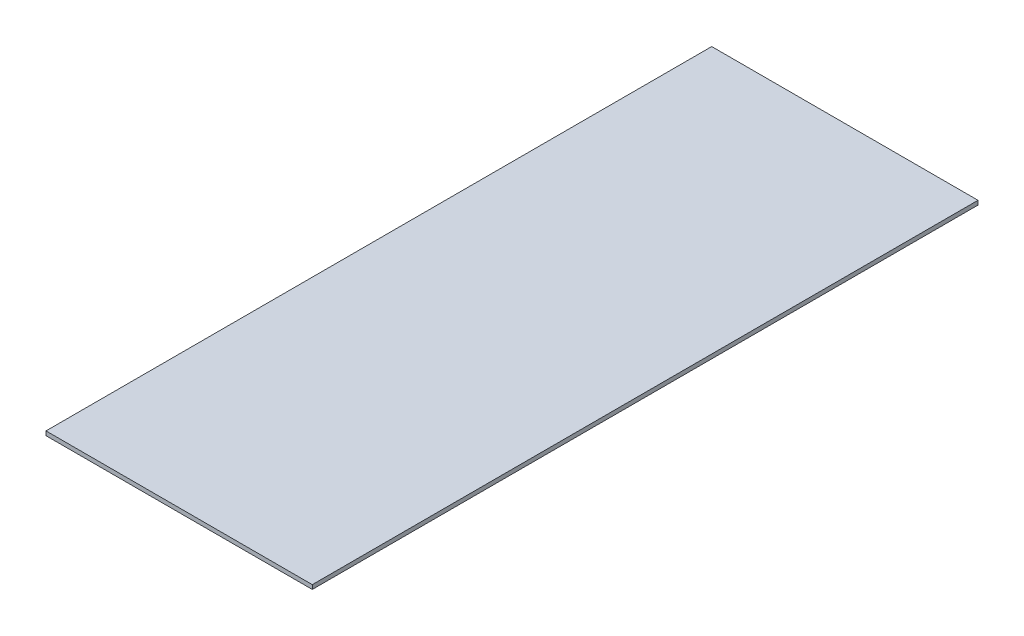
SolidWorks part; units mm, degrees
material "ABS"
ref_plane "Front Plane" through (0, 0, 0) normal (0, 0, 1) x (1, 0, 0)
ref_plane "Top Plane" through (0, 0, 0) normal (0, 1, 0) x (1, 0, 0)
ref_plane "Right Plane" through (0, 0, 0) normal (1, 0, 0) x (0, 0, -1)
sketch "Sketch1" plane through (0, 0, 0) normal (0, 1, 0) x (1, 0, 0)
  line L1 (0, 0) -> (202, 0)
  line L2 (0, 0) -> (0, 505)
  line L3 (0, 505) -> (202, 505)
  line L4 (202, 0) -> (202, 505)
  dimension "D1" = 202
  dimension "D2" = 505
extrude "Boss-Extrude1" add sketch "Sketch1" along normal blind 3.175
equation "\"ABS_thickness\" = 1.59\t"
equation "\"ABS_thickness_1/8\" = 3.175\t"
equation "\"Bus_bar_thickness\" = 3.175"
equation "\"Connector_width\" = 20.2"
equation "\"Number_of_cells_long\" = 25"
equation "\"Number_of_cells_wide\" = 2"
equation "\"Cell_height\" = 65.0"
equation "\"Cell_diam\" = 18.0"
equation "\"D1@Sketch1\"=\"Connector_width\"*10"
equation "\"D2@Sketch1\"=\"Connector_width\"*25"
equation "\"D1@Boss-Extrude1\"=\"ABS_thickness_1/8\""
